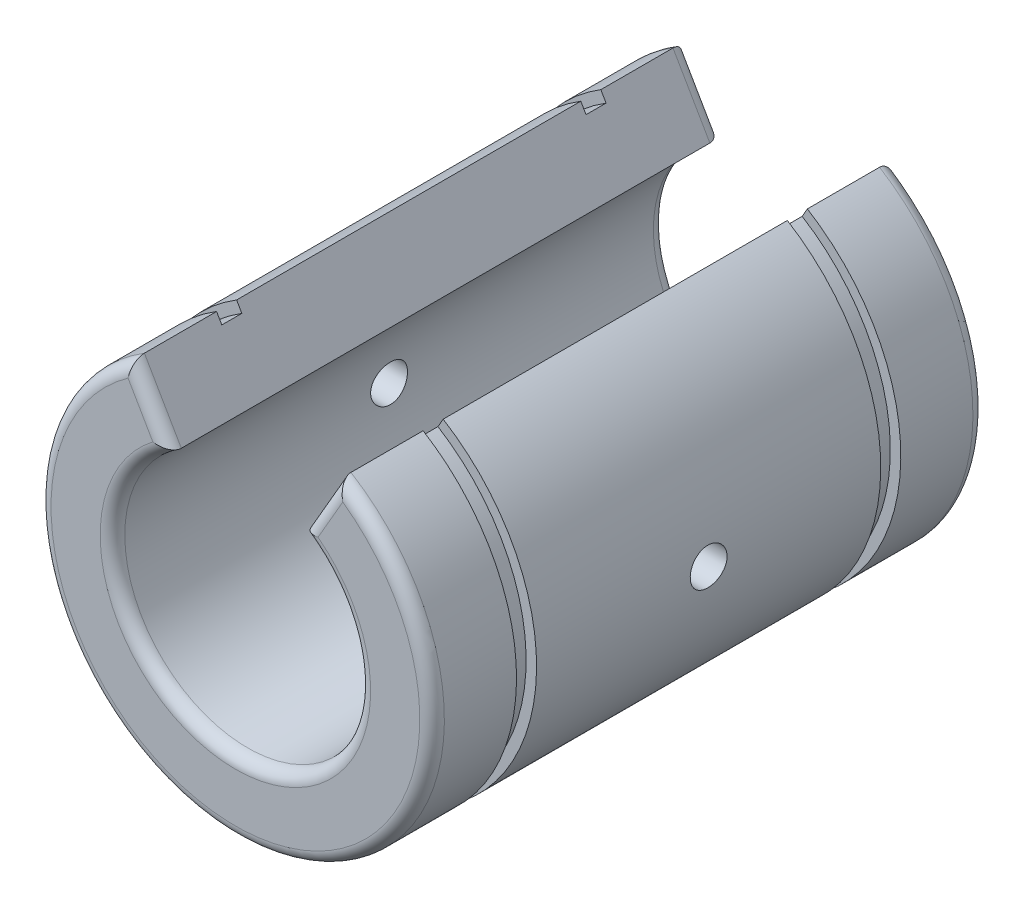
SolidWorks part; units mm, degrees
ref_plane "Front" through (0, 0, 0) normal (0, 0, 1) x (1, 0, 0)
ref_plane "Top" through (0, 0, 0) normal (0, 1, 0) x (1, 0, 0)
ref_plane "Right" through (0, 0, 0) normal (1, 0, 0) x (0, 0, -1)
sketch "Sketch1" plane through (0, 0, 0) normal (0, 0, 1) x (1, 0, 0)
  line L0 (5.4, 8.4167) -> (8.4021, 13.6164)
  line L1 (-5.4, 19.437) -> (5.4, 19.437) construction
  line L2 (-5.4, 19.437) -> (-5.4, 0) construction
  line L3 (-5.4, 0) -> (5.4, 0) construction
  line L4 (5.4, 19.437) -> (5.4, 0) construction
  line L5 (0, 0) -> (0, 22.9306) construction
  line L6 (-5.4, 8.4167) -> (-8.4021, 13.6164)
  arc A0 (-8.4021, 13.6164) -> (8.4021, 13.6164) centre (0, 0) ccw
  arc A1 (-5.4, 8.4167) -> (5.4, 8.4167) centre (0, 0) ccw
  point P8 (0, 0)
  dimension "D1" = 32
  dimension "D2" = 20
  dimension "D3" = 10.8
  dimension "D4" = 30
extrude "Extrude1" add sketch "Sketch1" along normal mid plane 45
ref_plane "Plane1" through (0, 0, 14) normal (0, 0, 1) x (1, 0, 0)
sketch "Sketch2" plane through (0, 0, 14) normal (0, 0, 1) x (1, 0, 0)
  circle A0 centre (0, 0) radius 16
  circle A1 centre (0, 0) radius 15.15
  arc A2 (-8.4021, 13.6164) -> (8.4021, 13.6164) centre (0, 0) ccw construction
  dimension "D1" = 30.3
extrude "Extrude2" cut sketch "Sketch2" along normal blind 1.63
fillet "Fillet1" radius 1 8 edges at (6.901, 11.0165, 22.5) (0, -16, 22.5) (-6.901, 11.0165, 22.5) (0, -10, 22.5) (-6.901, 11.0165, -22.5) (0, -16, -22.5) (6.901, 11.0165, -22.5) (0, -10, -22.5)
mirror "Mirror1" about plane through (0, 0, 0) normal (0, 0, 1) of "Extrude2"
sketch "Sketch3" plane through (0, 0, 0) normal (1, 0, 0) x (0, 0, -1)
  circle A0 centre (0, 0) radius 1.5
  dimension "D1" = 3
extrude "Extrude3" cut sketch "Sketch3" against normal through all and the other way through all
